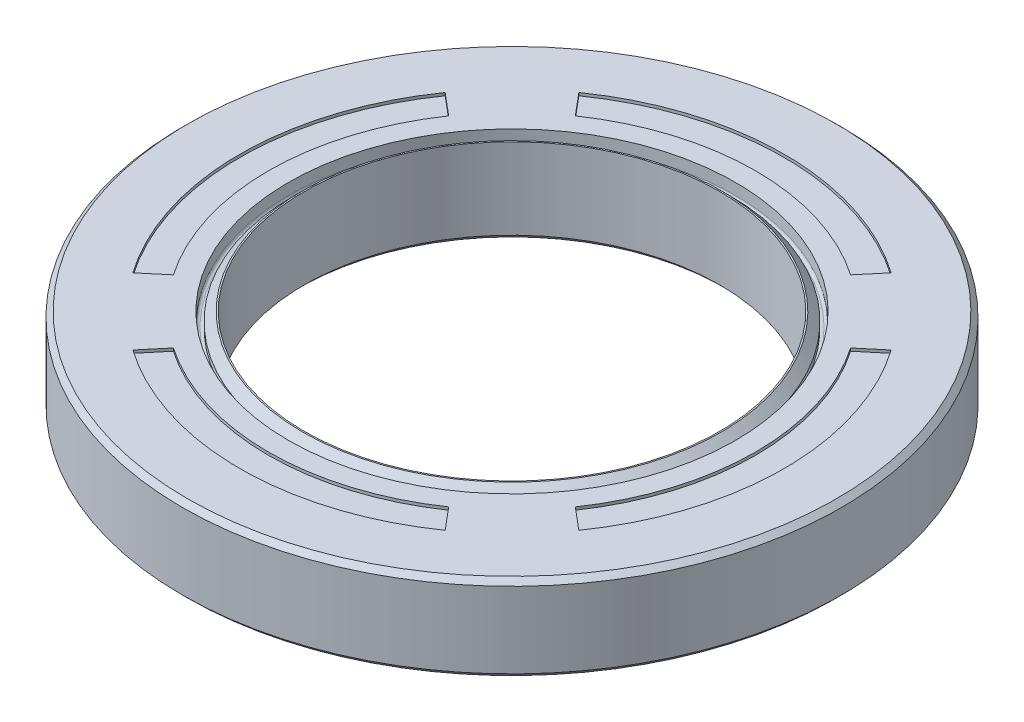
SolidWorks part; units mm, degrees
ref_plane "Front Plane" through (0, 0, 0) normal (0, 0, 1) x (1, 0, 0)
ref_plane "Top Plane" through (0, 0, 0) normal (0, 1, 0) x (1, 0, 0)
ref_plane "Right Plane" through (0, 0, 0) normal (1, 0, 0) x (0, 0, -1)
sketch "Sketch1" plane through (0, 0, 0) normal (0, 0, 1) x (1, 0, 0)
  line L0 (0, 10.7721) -> (0, -10.7721) construction
  line L1 (14.5, 3.8877) -> (14.5, -1.4052)
  line L4 (14.8536, -1.7588) -> (17.5, -1.7588)
  line L5 (23, 3.8877) -> (23, -1.4052)
  line L6 (17.5, -1.7588) -> (17.5, 2.5412)
  line L7 (17.5, 2.5412) -> (21, 2.5412)
  line L8 (21, 2.5412) -> (21, -1.7588)
  line L9 (22.6464, 4.2412) -> (23, 3.8877)
  line L10 (23, -1.4052) -> (22.6464, -1.7588)
  line L11 (14.5, -1.4052) -> (14.8536, -1.7588)
  line L13 (14.5, 4.2412) -> (14.6, 4.2412)
  line L14 (21, -1.7588) -> (22.6464, -1.7588)
  line L15 (14.5, 3.8877) -> (14.5, 4.2412)
  line L16 (14.5, 4.2412) -> (14.6, 4.2412)
  line L17 (14.6, 4.2412) -> (15.2, 3.6412)
  line L18 (15.2, 3.6412) -> (15.2, 3.2412)
  line L19 (15.2, 3.2412) -> (15.4, 3.2412)
  line L20 (15.6, 3.4412) -> (15.6, 4.2412)
  line L21 (14.6, 4.2412) -> (14.5, 4.2412)
  line L22 (15.6, 4.2412) -> (22.6464, 4.2412)
  arc A1 (15.4, 3.2412) -> (15.6, 3.4412) centre (15.4, 3.4412) ccw
  point P0 (0, 0)
  point P5 (0, 0)
  dimension "D15" = 0.2
  dimension "D1" = 14.5
  dimension "D2" = 17.5
  dimension "D3" = 23
  dimension "D4" = 3.5
  dimension "D5" = 4.3
  dimension "D6" = 0.1
  dimension "D7" = 0.4
  dimension "D8" = 0.5
  dimension "D9" = 45
  dimension "D10" = 0.5
  dimension "D11" = 45
  dimension "D12" = 0.5
  dimension "D13" = 0.4
  dimension "D14" = 1
  dimension "D16" = 1
revolve "Revolve1" add sketch "Sketch1" angle 360 about L0
sketch "Sketch2" plane through (0, 4.2412, 0) normal (0, 1, 0) x (1, 0, 0)
  line L5 (-14.0253, -9.6069) -> (-15.5639, -10.898)
  line L6 (-14.0253, 9.6069) -> (-15.5639, 10.898)
  arc A0 (-15.5639, 10.898) -> (-15.5639, -10.898) centre (0, 0) ccw
  arc A1 (-14.0253, 9.6069) -> (-14.0253, -9.6069) centre (0, 0) ccw
  point P7 (0, 0)
  point P10 (0, 0)
  point P16 (0, 0)
  point P18 (0, 0)
  point P21 (0.5757, 0)
  dimension "D1" = 38
  dimension "D2" = 34
extrude "Cut-Extrude1" cut sketch "Sketch2" against normal blind 0.2
pattern_circular "CirPattern1" count 4 over 360 about axis through (0, 0, 0) along (0, 1, 0) of "Cut-Extrude1"
